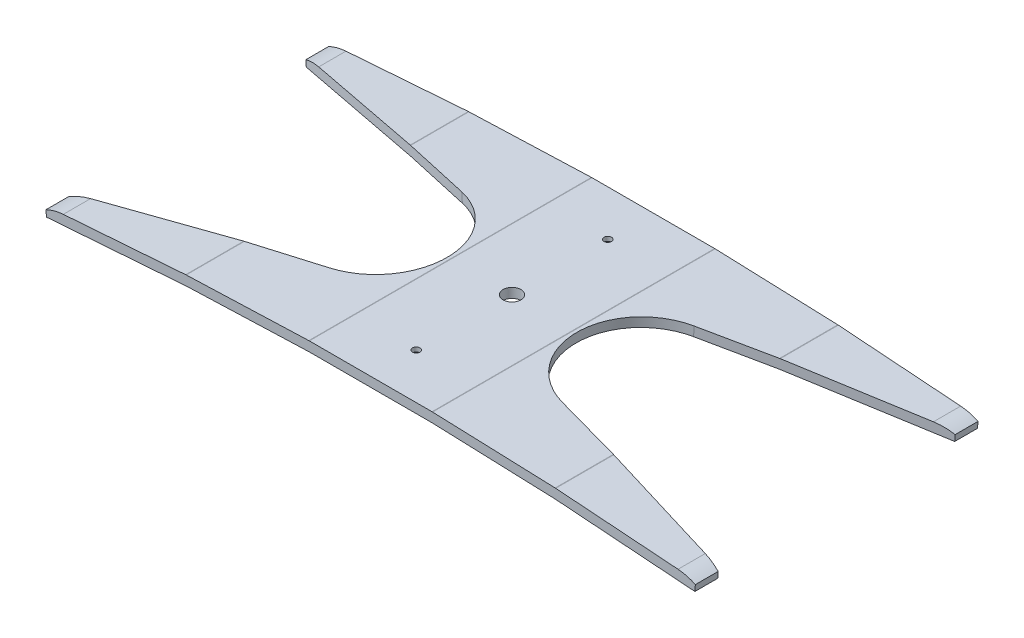
SolidWorks part; units mm, degrees
material "MARAGING STEEL C250"
ref_plane "Front Plane" through (0, 0, 0) normal (0, 0, 1) x (1, 0, 0)
ref_plane "Top Plane" through (0, 0, 0) normal (0, 1, 0) x (1, 0, 0)
ref_plane "Right Plane" through (0, 0, 0) normal (1, 0, 0) x (0, 0, -1)
sketch "Sketch6" plane through (0, 0, 0) normal (0, 0, 1) x (1, 0, 0)
  line L0 (0, 0) -> (0, 5.08)
  line L1 (165.7074, -2.3868) -> (161.1203, -27.3692) construction
  line L2 (0, 0) -> (32.5257, 0)
  line L3 (0, 5.08) -> (0, 10.16) construction
  line L4 (32.6181, -0.0017) -> (65.1222, -1.1849)
  line L5 (32.8029, 5.075) -> (65.307, 3.8917)
  line L6 (65.1222, -1.1849) -> (97.6263, -2.3681)
  line L7 (98.088, 2.6934) -> (130.5275, 0.3285)
  line L8 (97.7186, -2.3732) -> (130.1582, -4.7381)
  line L9 (65.307, 3.8917) -> (97.8111, 2.7085)
  line L10 (130.5275, 0.3285) -> (162.9671, -2.0364)
  line L11 (130.1582, -4.7381) -> (171.909, -7.7818)
  line L12 (130.5275, 0.3285) -> (130.3429, -2.2048) construction
  line L13 (130.3429, -2.2048) -> (130.1582, -4.7381) construction
  line L14 (0, 5.08) -> (32.5257, 5.08)
  line L15 (65.307, 3.8917) -> (65.2146, 1.3534) construction
  line L16 (65.2146, 1.3534) -> (65.1222, -1.1849) construction
  line L17 (161.1203, -27.3692) -> (165.1, -2.2829) construction
  line L20 (162.9671, -2.0364) -> (162.5977, -7.103) construction
  line L24 (171.909, -7.7818) -> (172.1491, -4.4885)
  arc A2 (0, -6.35) -> (328.3602, -68.4979) centre (0, -904.875) cw construction
  arc A3 (0, 12.7) -> (329.4676, -48.4901) centre (0, -904.875) cw construction
  arc A4 (97.6263, -2.3681) -> (97.7186, -2.3732) centre (97.5339, -4.9065) cw
  arc A5 (32.5257, 0) -> (32.6181, -0.0017) centre (32.5257, -2.54) cw
  arc A6 (97.8111, 2.7085) -> (98.088, 2.6934) centre (97.5339, -4.9065) cw
  arc A7 (32.5257, 5.08) -> (32.8029, 5.075) centre (32.5257, -2.54) cw
  arc A8 (0, 2.54) -> (231.9864, -12.5338) centre (0, -1790.1394) cw construction
  arc A9 (162.9671, -2.0364) -> (172.1491, -4.4885) centre (161.1203, -27.3692) cw
  arc A10 (0, -8.89) -> (327.432, -70.8622) centre (0, -904.875) cw construction
  point P8 (-165.1, -2.2829)
  dimension "D1" = 25.4
  dimension "D2" = 1792.6794
  dimension "D3" = 917.575
  dimension "D4" = 898.525
  dimension "D5" = 5.08
  dimension "D6" = 330.2
  dimension "D7" = 6.35
  dimension "D9" = 2.54
  dimension "D10" = 6.235
  dimension "D12" = 895.985
  dimension "D8" = 7.62
  dimension "D11" = 1.39
  dimension "D13" = 3.302
extrude "Boss-Extrude1" add sketch "Sketch6" against normal mid plane 149.86
sketch "Sketch11" plane through (0.3445, 4.7255, 0) normal (0.0727, 0.9974, 0) x (0.9974, -0.0727, 0)
  line L0 (172.0198, 0) -> (69.9886, 0) construction
  line L1 (172.0198, 74.93) -> (172.0198, -74.93) construction
  line L2 (172.0198, 62.8317) -> (172.0198, -62.8317)
  line L3 (172.0198, 62.8317) -> (61.1975, 34.9802)
  line L4 (162.6838, -74.93) -> (97.6325, -74.93) construction
  line L5 (172.0198, -62.8317) -> (61.1975, -34.9802)
  line L6 (-0.3694, 74.93) -> (-0.3694, -74.93) construction
  arc A0 (61.1975, 34.9802) -> (61.1975, -34.9802) centre (69.9886, 0) ccw
  dimension "D1" = 34.29
  dimension "D2" = 36.068
  dimension "D3" = 12.0983
extrude "Cut-Extrude1" cut sketch "Sketch11" along normal through all and the other way through all
mirror "Mirror1" about plane through (0, 0, 0) normal (1, 0, 0) of "Cut-Extrude1", "Boss-Extrude1"
hole_wizard "5/32 (0.15625) Diameter Hole1" positions "Sketch13" profile "Sketch12" hole size "5/32" standard "ANSI Inch" end condition up to next
sketch "Sketch13" plane through (-1.8628, 0, 42.8486) normal (0, 1, 0) x (1, 0, 0)
  line L1 (1.8628, 93.6486) -> (1.8628, -7.9514) construction
  point P0 (1.8628, 93.6486)
  point P15 (1.8628, -7.9514)
  dimension "D1" = 101.6
sketch "Sketch12" plane through (0, 0, -50.8) normal (1, 0, 0) x (0, 0, -1)
  line L0 (0, 0) -> (0, 5.08)
  line L1 (0, 5.08) -> (1.9844, 5.08)
  line L2 (1.9844, 5.08) -> (1.9844, 2.8107)
  line L3 (1.9844, 2.8107) -> (5.334, 0)
  line L5 (5.334, 0) -> (0, 0)
  line L6 (-1.9844, 2.8107) -> (-5.334, 0) construction
  line L11 (0, -6.35) -> (0, 107.95) construction
  dimension "Thru Hole Dia." = 3.9688
  dimension "Thru Hole Depth" = 5.08
  dimension "Near C'Sink Dia." = 10.668
  dimension "Near C'Sink Angle" = 100
hole_wizard "3/8 (0.375) Diameter Hole1" positions "Sketch16" profile "Sketch15" hole size "3/8" standard "ANSI Inch" end condition up to next
sketch "Sketch16" plane through (0, 5.08, 0) normal (0, 1, 0) x (1, 0, 0)
  point P0 (0, 0)
sketch "Sketch15" plane through (0, 5.08, 0) normal (1, 0, 0) x (0, 0, 1)
  line L0 (0, 0) -> (0, 5.08)
  line L1 (0, 5.08) -> (4.7625, 5.08)
  line L2 (4.7625, 5.08) -> (4.7625, 0)
  line L5 (4.7625, 0) -> (0, 0)
  line L11 (0, -6.35) -> (0, 107.95) construction
  dimension "Thru Hole Dia." = 9.525
  dimension "Thru Hole Depth" = 5.08
